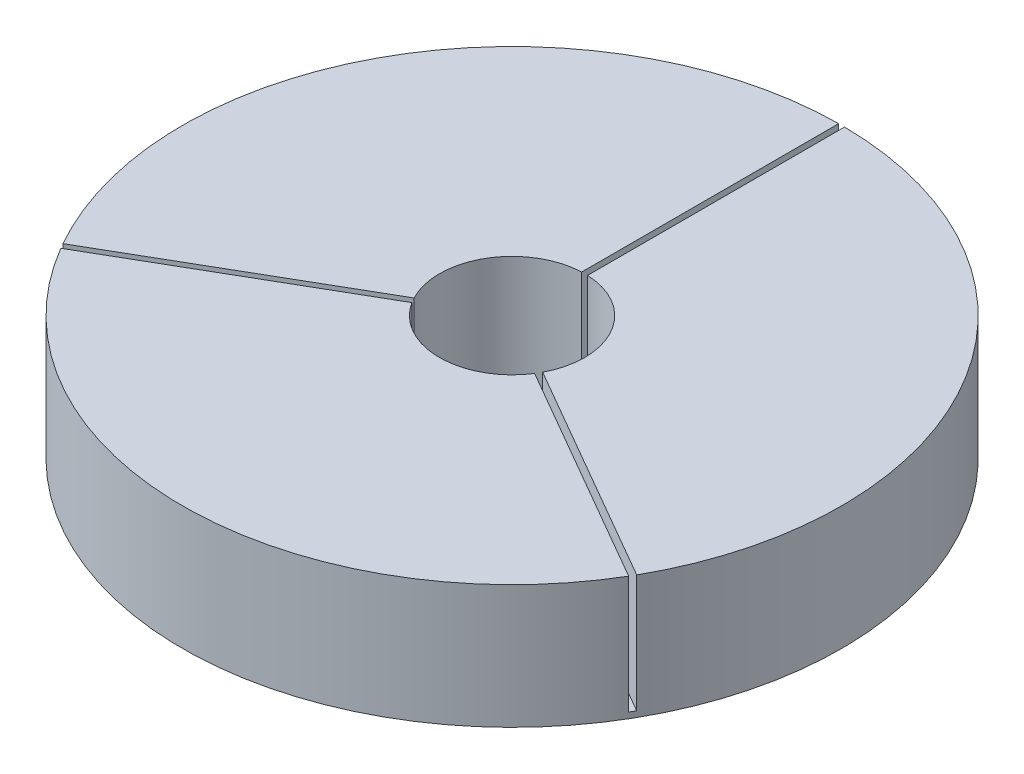
SolidWorks part; units mm, degrees
ref_plane "Front Plane" through (0, 0, 0) normal (0, 0, 1) x (1, 0, 0)
ref_plane "Top Plane" through (0, 0, 0) normal (0, 1, 0) x (1, 0, 0)
ref_plane "Right Plane" through (0, 0, 0) normal (1, 0, 0) x (0, 0, -1)
sketch "Sketch2" plane through (0, 0, 0) normal (0, 1, 0) x (1, 0, 0)
  line L0 (0, 212.8341) -> (0, -234.9862) construction
  line L1 (-286.0229, 0) -> (307.7407, 0) construction
  line L2 (309.5461, -175.0504) -> (1.5875, 2.7496)
  line L3 (-3.175, 355.6) -> (3.175, 355.6)
  line L4 (-3.175, 355.6) -> (-3.175, 0)
  line L5 (-3.175, 0) -> (3.175, 0)
  line L6 (3.175, 355.6) -> (3.175, 0)
  line L7 (-3.175, 355.6) -> (3.175, 0) construction
  line L8 (-3.175, 0) -> (3.175, 355.6) construction
  line L9 (309.5461, -175.0504) -> (306.3711, -180.5496)
  line L10 (306.3711, -180.5496) -> (-1.5875, -2.7496)
  line L11 (1.5875, 2.7496) -> (-1.5875, -2.7496)
  line L12 (-306.3711, -180.5496) -> (1.5875, -2.7496)
  line L13 (-306.3711, -180.5496) -> (-309.5461, -175.0504)
  line L14 (-309.5461, -175.0504) -> (-1.5875, 2.7496)
  line L15 (1.5875, -2.7496) -> (-1.5875, 2.7496)
  circle A0 centre (0, 0) radius 78.359
  circle A1 centre (0, 0) radius 355.6142
  point P7 (0, 177.8)
  point P22 (0, 0)
  dimension "D1" = 156.718
  dimension "D2" = 355.6
  dimension "D3" = 6.35
  dimension "D4" = 3
extrude "Boss-Extrude1" add sketch "Sketch2" along normal blind 127 contours L4 A1 L14 A0 | L2 A1 L6 A0 | L12 A1 L10 A0
sketch "Sketch3" plane through (0, 0, 0) normal (0, -1, 0) x (1, 0, 0)
  circle A0 centre (0, 0) radius 355.6142
extrude "Boss-Extrude2" add sketch "Sketch3" along normal blind 6.35
